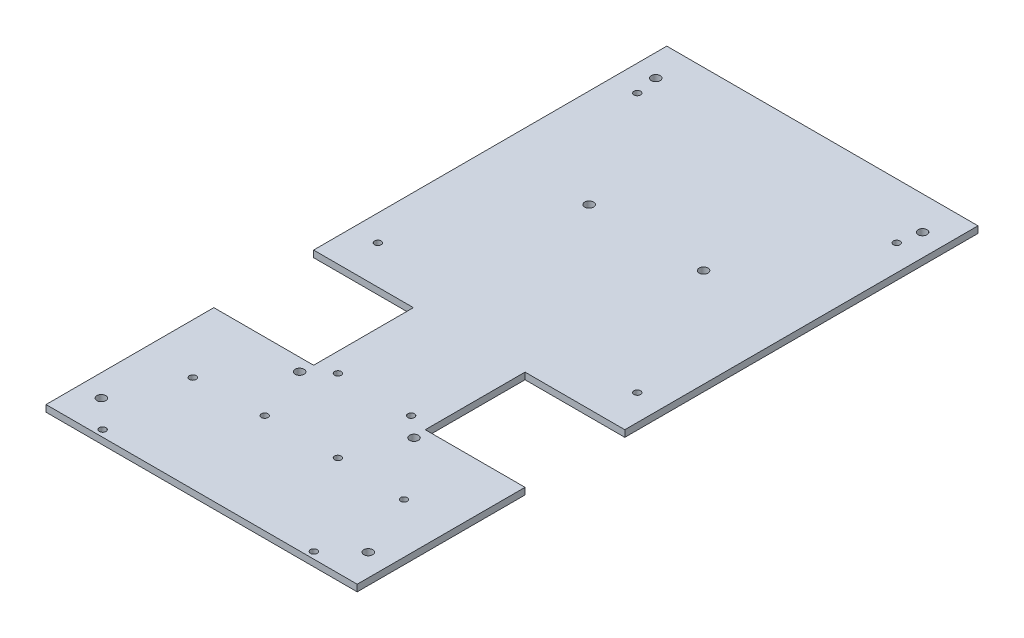
SolidWorks part; units mm, degrees
material "PMMA"
ref_plane "Front Plane" through (0, 0, 0) normal (0, 0, 1) x (1, 0, 0)
ref_plane "Top Plane" through (0, 0, 0) normal (0, 1, 0) x (1, 0, 0)
ref_plane "Right Plane" through (0, 0, 0) normal (1, 0, 0) x (0, 0, -1)
sketch "Schizzo1" plane through (0, 0, 0) normal (0, 1, 0) x (1, 0, 0)
  line L0 (-26.6704, 112.0472) -> (-26.6704, -167.9528) construction
  line L1 (-96.8504, 112.0472) -> (43.5096, 112.0472)
  line L2 (-96.8504, 112.0472) -> (-96.8504, -167.9528)
  line L3 (-96.8504, -167.9528) -> (43.5096, -167.9528)
  line L4 (43.5096, 112.0472) -> (43.5096, -167.9528)
  line L5 (-96.8504, -127.9528) -> (43.5096, -127.9528) construction
  line L6 (-96.8504, 12.0472) -> (43.5096, 12.0472) construction
  dimension "D1" = 280
  dimension "D2" = 140.36
  dimension "D3" = 40
  dimension "D4" = 100
extrude "Estrusione-Estrusione1" add sketch "Schizzo1" along normal blind 3
sketch "Schizzo2" plane through (0, 3, 0) normal (0, 1, 0) x (1, 0, 0)
  line L0 (-96.8504, 112.0472) -> (-96.8504, -167.9528) construction
  line L1 (-96.8504, -167.9528) -> (43.5096, -167.9528) construction
  line L2 (-26.6704, -167.9528) -> (-26.6704, 112.0472) construction
  line L3 (43.5096, 112.0472) -> (-96.8504, 112.0472) construction
  line L4 (-96.8504, -27.9528) -> (43.5096, -27.9528) construction
  line L5 (43.5096, -167.9528) -> (43.5096, 112.0472) construction
  circle A0 centre (-86.8504, -152.9528) radius 2
  circle A1 centre (33.5096, -152.9528) radius 2
  circle A2 centre (-86.8504, 97.0472) radius 2
  circle A3 centre (33.5096, 97.0472) radius 2
  point P16 (33.5096, 97.0472)
  dimension "D1" = 4
  dimension "D2" = 10
  dimension "D3" = 15
  dimension "D4" = 120.36
extrude "Taglio-Estrusione1" cut sketch "Schizzo2" along direction (0, 1, 0) on the side against the normal through all
sketch "Schizzo3" plane through (0, 0, 0) normal (0, 1, 0) x (1, 0, 0)
  line L0 (-96.8504, -92.2528) -> (43.5096, -92.2528) construction
  line L1 (-96.8504, 112.0472) -> (-96.8504, -167.9528) construction
  line L2 (43.5096, -167.9528) -> (43.5096, 112.0472) construction
  line L3 (-96.8504, -167.9528) -> (43.5096, -167.9528) construction
  line L4 (-26.6704, 112.0472) -> (-26.6704, -167.9528) construction
  line L5 (-96.8504, -92.2528) -> (-51.8504, -92.2528)
  line L6 (-96.8504, -92.2528) -> (-96.8504, -47.2528)
  line L7 (-96.8504, -47.2528) -> (-51.8504, -47.2528)
  line L8 (-51.8504, -92.2528) -> (-51.8504, -47.2528)
  line L9 (43.5096, 112.0472) -> (-96.8504, 112.0472) construction
  line L10 (43.5096, -92.2528) -> (43.5096, -47.2528)
  line L11 (43.5096, -92.2528) -> (-1.4904, -92.2528)
  line L12 (-1.4904, -92.2528) -> (-1.4904, -47.2528)
  line L13 (43.5096, -47.2528) -> (-1.4904, -47.2528)
  dimension "D1" = 75.7
  dimension "D2" = 45
  dimension "D3" = 45
extrude "Taglio-Estrusione2" cut sketch "Schizzo3" along direction (0, 1, 0) on the side of the normal through all
sketch "Schizzo4" plane through (0, 0, 0) normal (0, 1, 0) x (1, 0, 0)
  line L0 (-26.6704, 112.0472) -> (-26.6704, -167.9528) construction
  line L1 (-85.1704, 87.0472) -> (31.8296, 87.0472) construction
  line L2 (-85.1704, 87.0472) -> (-85.1704, -29.9528) construction
  line L3 (-85.1704, -29.9528) -> (31.8296, -29.9528) construction
  line L4 (31.8296, 87.0472) -> (31.8296, -29.9528) construction
  line L5 (43.5096, 112.0472) -> (-96.8504, 112.0472) construction
  line L6 (-96.8504, -167.9528) -> (43.5096, -167.9528) construction
  line L8 (-43.1804, -89.9528) -> (-10.1604, -89.9528) construction
  line L9 (-43.1804, -89.9528) -> (-43.1804, -122.9728) construction
  line L10 (-43.1804, -122.9728) -> (-10.1604, -122.9728) construction
  line L11 (-10.1604, -89.9528) -> (-10.1604, -122.9728) construction
  line L14 (-52.4704, 32.6472) -> (-0.8704, 32.6472) construction
  line L15 (-52.4704, 32.6472) -> (-52.4704, -97.9528) construction
  line L16 (-52.4704, -97.9528) -> (-0.8704, -97.9528) construction
  line L17 (-0.8704, 32.6472) -> (-0.8704, -97.9528) construction
  line L18 (-74.2954, -124.3128) -> (20.9546, -124.3128) construction
  line L19 (-74.2954, -124.3128) -> (-74.2954, -164.9528) construction
  line L20 (-74.2954, -164.9528) -> (20.9546, -164.9528) construction
  line L21 (20.9546, -124.3128) -> (20.9546, -164.9528) construction
  circle A0 centre (-85.1704, 87.0472) radius 1.5
  circle A1 centre (-85.1704, -29.9528) radius 1.5
  circle A2 centre (31.8296, -29.9528) radius 1.5
  circle A3 centre (31.8296, 87.0472) radius 1.5
  circle A4 centre (-43.1804, -89.9528) radius 1.5
  circle A5 centre (-10.1604, -89.9528) radius 1.5
  circle A6 centre (-10.1604, -122.9728) radius 1.5
  circle A7 centre (-43.1804, -122.9728) radius 1.5
  circle A8 centre (-52.4704, -97.9528) radius 2
  circle A9 centre (-0.8704, -97.9528) radius 2
  circle A10 centre (-0.8704, 32.6472) radius 2
  circle A11 centre (-52.4704, 32.6472) radius 2
  circle A12 centre (-74.2954, -124.3128) radius 1.5
  circle A13 centre (20.9546, -124.3128) radius 1.5
  circle A14 centre (20.9546, -164.9528) radius 1.5
  circle A15 centre (-74.2954, -164.9528) radius 1.5
  point P4 (-26.6704, 87.0472)
  point P19 (-26.6704, -89.9528)
  point P24 (-26.6704, 32.6472)
  point P37 (-26.6704, -124.3128)
  dimension "D4" = 3
  dimension "D5" = 33.02
  dimension "D7" = 3
  dimension "D8" = 60
  dimension "D12" = 4
  dimension "D13" = 95.25
  dimension "D16" = 3
  dimension "D1" = 117
  dimension "D2" = 117
  dimension "D3" = 25
  dimension "D6" = 33.02
  dimension "D9" = 51.6
  dimension "D10" = 130.6
  dimension "D11" = 70
  dimension "D14" = 40.64
  dimension "D15" = 3
extrude "Taglio-Estrusione3" cut sketch "Schizzo4" along direction (0, 1, 0) on the side of the normal through all
equation "\"Thickness2\"= 2"
equation "\"Thickness3\"=3"
equation "\"D1@Estrusione-Estrusione1\"=\"Thickness3\""
